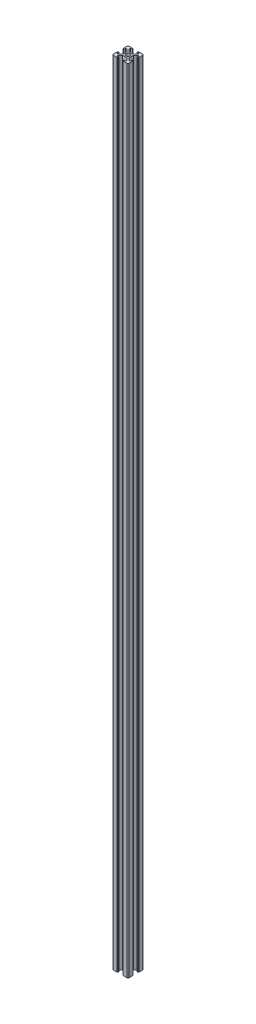
SolidWorks part; units mm, degrees
ref_plane "前视基准面" through (0, 0, 0) normal (0, 0, 1) x (1, 0, 0)
ref_plane "上视基准面" through (0, 0, 0) normal (0, 1, 0) x (1, 0, 0)
ref_plane "右视基准面" through (0, 0, 0) normal (1, 0, 0) x (0, 0, -1)
other "Configuration Table"
sketch "草图1" plane through (0, 0, 0) normal (0, 0, 1) x (1, 0, 0)
  line L0 (0, 0) -> (0, 1000)
  dimension "D1" = 1000
other "铝型材 20 X 20 X R1.5(1)"
ref_plane "基准面1" through (0, 0, 0) normal (0, 1, 0) x (-1, 0, 0)
sketch "Sketch1" plane through (0, 0, 0) normal (0, 1, 0) x (-1, 0, 0)
  line L0 (-3.6, 10) -> (-3.6, 9.5)
  line L1 (-3.6, 9.5) -> (-3.1, 9.5)
  line L2 (-3.1, 9.5) -> (-3.1, 8.5)
  line L3 (-3.1, 8.5) -> (-5.5, 8.5)
  line L4 (-8.5, -10) -> (-3.6, -10)
  line L5 (-10, -8.5) -> (-10, -3.6)
  line L6 (8.5, 10) -> (3.6, 10)
  line L7 (10, 8.5) -> (10, 3.6)
  line L8 (0, 14.8756) -> (0, 0) construction
  line L9 (0, 0) -> (14.1675, 0) construction
  line L10 (-5.5, 8.5) -> (-5.5, 6.65)
  line L11 (-5.5, 6.65) -> (-2.75, 3.9)
  line L12 (-2.75, 3.9) -> (2.75, 3.9)
  line L13 (5.5, 6.65) -> (2.75, 3.9)
  line L14 (5.5, 8.5) -> (5.5, 6.65)
  line L15 (3.1, 8.5) -> (5.5, 8.5)
  line L16 (3.1, 9.5) -> (3.1, 8.5)
  line L17 (3.6, 9.5) -> (3.1, 9.5)
  line L18 (3.6, 10) -> (3.6, 9.5)
  line L19 (-3.6, 10) -> (-8.5, 10)
  line L20 (10, 3.6) -> (9.5, 3.6)
  line L21 (9.5, 3.6) -> (9.5, 3.1)
  line L22 (9.5, 3.1) -> (8.5, 3.1)
  line L23 (8.5, 3.1) -> (8.5, 5.5)
  line L24 (8.5, 5.5) -> (6.65, 5.5)
  line L25 (6.65, 5.5) -> (3.9, 2.75)
  line L26 (3.9, 2.75) -> (3.9, -2.75)
  line L27 (6.65, -5.5) -> (3.9, -2.75)
  line L28 (8.5, -5.5) -> (6.65, -5.5)
  line L29 (8.5, -3.1) -> (8.5, -5.5)
  line L30 (9.5, -3.1) -> (8.5, -3.1)
  line L31 (9.5, -3.6) -> (9.5, -3.1)
  line L32 (10, -3.6) -> (9.5, -3.6)
  line L33 (3.6, -10) -> (3.6, -9.5)
  line L34 (3.6, -9.5) -> (3.1, -9.5)
  line L35 (3.1, -9.5) -> (3.1, -8.5)
  line L36 (3.1, -8.5) -> (5.5, -8.5)
  line L37 (5.5, -8.5) -> (5.5, -6.65)
  line L38 (5.5, -6.65) -> (2.75, -3.9)
  line L39 (2.75, -3.9) -> (-2.75, -3.9)
  line L40 (-5.5, -6.65) -> (-2.75, -3.9)
  line L41 (-5.5, -8.5) -> (-5.5, -6.65)
  line L42 (-3.1, -8.5) -> (-5.5, -8.5)
  line L43 (-3.1, -9.5) -> (-3.1, -8.5)
  line L44 (-3.6, -9.5) -> (-3.1, -9.5)
  line L45 (-3.6, -10) -> (-3.6, -9.5)
  line L46 (-10, -3.6) -> (-9.5, -3.6)
  line L47 (-9.5, -3.6) -> (-9.5, -3.1)
  line L48 (-9.5, -3.1) -> (-8.5, -3.1)
  line L49 (-8.5, -3.1) -> (-8.5, -5.5)
  line L50 (-8.5, -5.5) -> (-6.65, -5.5)
  line L51 (-6.65, -5.5) -> (-3.9, -2.75)
  line L52 (-3.9, -2.75) -> (-3.9, 2.75)
  line L53 (-6.65, 5.5) -> (-3.9, 2.75)
  line L54 (-8.5, 5.5) -> (-6.65, 5.5)
  line L55 (-8.5, 3.1) -> (-8.5, 5.5)
  line L56 (-9.5, 3.1) -> (-8.5, 3.1)
  line L57 (-9.5, 3.6) -> (-9.5, 3.1)
  line L58 (-10, 3.6) -> (-9.5, 3.6)
  line L59 (3.6, -10) -> (8.5, -10)
  line L60 (-10, 3.6) -> (-10, 8.5)
  line L61 (10, -3.6) -> (10, -8.5)
  circle A0 centre (0, 0) radius 2.5
  arc A1 (-10, 8.5) -> (-8.5, 10) centre (-8.5, 8.5) cw
  arc A2 (10, 8.5) -> (8.5, 10) centre (8.5, 8.5) ccw
  arc A3 (-8.5, -10) -> (-10, -8.5) centre (-8.5, -8.5) cw
  arc A4 (8.5, -10) -> (10, -8.5) centre (8.5, -8.5) ccw
  point P0 (-10, 0)
  point P1 (10, 0)
  point P2 (0, 10)
  point P3 (0, -10)
  point P4 (0, 0)
  point P5 (-10, -10)
  point P6 (10, -10)
  point P7 (10, 10)
  point P8 (-10, 10)
  point P13 (0, 0)
  point P36 (-10, 10)
  point P39 (10, 10)
  dimension "D1" = 11
  dimension "D2" = 20
  dimension "D3" = 6.2
  dimension "D4" = 7.2
  dimension "D5" = 6.1
  dimension "D6" = 5
  dimension "D7" = 1.5
  dimension "D8" = 45
  dimension "D9" = 0.5
  dimension "D10" = 1
  dimension "D11" = 5.5
